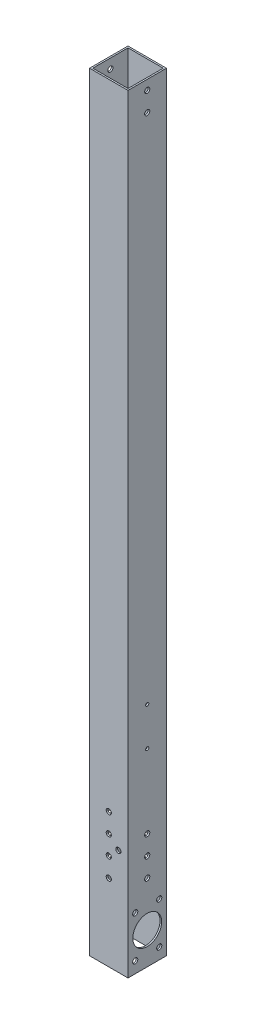
SolidWorks part; units mm, degrees
material "6061-T6 (SS)"
ref_plane "Front Plane" through (0, 0, 0) normal (0, 0, 1) x (1, 0, 0)
ref_plane "Top Plane" through (0, 0, 0) normal (0, 1, 0) x (1, 0, 0)
ref_plane "Right Plane" through (0, 0, 0) normal (1, 0, 0) x (0, 0, -1)
sketch "Sketch1" plane through (0, 0, 0) normal (0, 1, 0) x (1, 0, 0)
  line L0 (17.4625, 17.4625) -> (-17.4625, 17.4625)
  line L1 (19.05, -19.05) -> (-19.05, -19.05)
  line L2 (19.05, -19.05) -> (19.05, 19.05)
  line L3 (19.05, 19.05) -> (-19.05, 19.05)
  line L4 (-19.05, -19.05) -> (-19.05, 19.05)
  line L5 (19.05, -19.05) -> (-19.05, 19.05) construction
  line L6 (19.05, 19.05) -> (-19.05, -19.05) construction
  line L7 (-17.4625, -17.4625) -> (-17.4625, 17.4625)
  line L8 (17.4625, -17.4625) -> (-17.4625, -17.4625)
  line L9 (17.4625, -17.4625) -> (17.4625, 17.4625)
  point P0 (0, 0)
  dimension "D1" = 38.1
  dimension "D2" = 1.5875
extrude "Boss-Extrude1" add sketch "Sketch1" along normal blind 762
sketch "Sketch2" plane through (0, 0, 19.05) normal (0, 0, 1) x (1, 0, 0)
  line L1 (-19.05, 0) -> (19.05, 0) construction
  line L2 (0, 114.3) -> (9.525, 104.775) construction
  line L3 (9.525, 104.775) -> (0, 95.25) construction
  circle A0 centre (0, 76.2) radius 2.5527
  circle A1 centre (0, 95.25) radius 2.5527
  circle A4 centre (0, 114.3) radius 2.5527
  circle A5 centre (0, 133.35) radius 2.5527
  circle A7 centre (9.525, 104.775) radius 2.5527
  point P16 (0, 0)
  dimension "D4" = 19.05
  dimension "D5" = 76.2
  dimension "D6" = 19.05
  dimension "D7" = 19.05
  dimension "D8" = 9.525
extrude "Cut-Extrude1" cut sketch "Sketch2" against normal through all
sketch "Sketch3" plane through (19.05, 0, 0) normal (1, 0, 0) x (0, 0, -1)
  line L0 (-19.05, 0) -> (19.05, 0) construction
  line L1 (0, 225.425) -> (0, 187.325) construction
  line L2 (-19.05, 225.425) -> (19.05, 225.425) construction
  line L3 (-19.05, 762) -> (-19.05, 0) construction
  line L4 (19.05, 762) -> (19.05, 0) construction
  line L5 (-19.05, 762) -> (19.05, 762) construction
  circle A0 centre (0, 76.2) radius 2.5527
  circle A1 centre (0, 95.25) radius 2.5527
  circle A2 centre (0, 114.3) radius 2.5527
  circle A4 centre (0, 225.425) radius 1.5875
  circle A7 centre (0, 187.325) radius 1.5875
  circle A9 centre (0, 752.475) radius 2.5527
  circle A10 centre (0, 733.425) radius 2.5527
  point P10 (0, 0)
  point P11 (0, 206.375)
  dimension "D1" = 19.05
  dimension "D2" = 19.05
  dimension "D3" = 19.05
  dimension "D4" = 5.1054
  dimension "D5" = 3.175
  dimension "D7" = 38.1
  dimension "D10" = 9.525
  dimension "D6" = 206.375
extrude "Cut-Extrude2" cut sketch "Sketch3" against normal through all
sketch "Sketch4" plane through (19.05, 0, 0) normal (1, 0, 0) x (0, 0, -1)
  line L0 (-19.05, 0) -> (19.05, 0) construction
  circle A0 centre (0, 31.75) radius 14.2875
  circle A1 centre (-11.9063, 52.3722) radius 2.5527
  circle A2 centre (11.9063, 52.3722) radius 2.5527
  circle A3 centre (11.9063, 11.1278) radius 2.5527
  circle A4 centre (-11.9063, 11.1278) radius 2.5527
  circle A5 centre (0, 31.75) radius 23.8125 construction
  point P16 (0, 0)
  dimension "D1" = 5.1054
  dimension "D2" = 47.625
  dimension "D3" = 60
  dimension "D4" = 31.75
  dimension "D5" = 28.575
extrude "Cut-Extrude3" cut sketch "Sketch4" against normal through all
